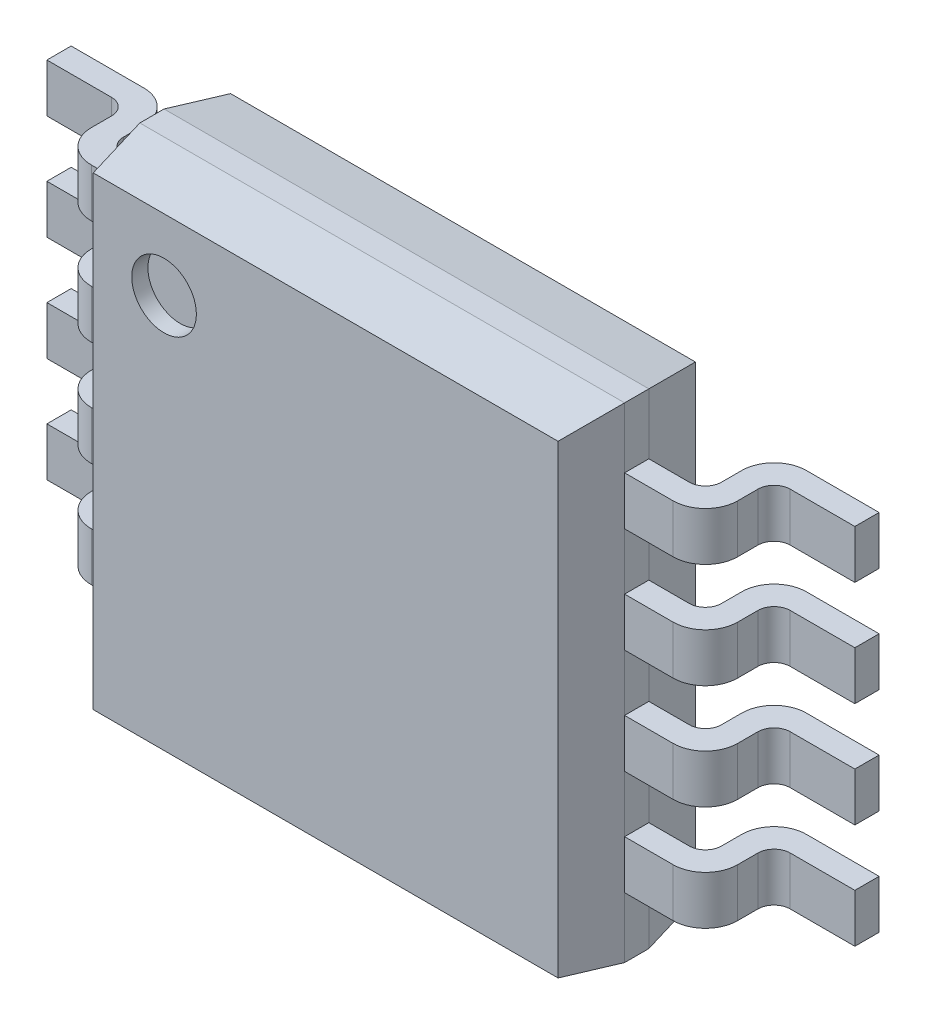
SolidWorks part; units mm, degrees
ref_plane "Спереди" through (0, 0, 0) normal (0, 0, 1) x (1, 0, 0)
ref_plane "Сверху" through (0, 0, 0) normal (0, 1, 0) x (1, 0, 0)
ref_plane "Справа" through (0, 0, 0) normal (1, 0, 0) x (0, 0, -1)
ref_plane "Плоскость1" through (0, 0, 0.075) normal (0, 0, 1) x (1, 0, 0)
sketch "Эскиз1" plane through (0, 0, 0.075) normal (0, 0, 1) x (1, 0, 0)
  line L1 (1.5, 1.5) -> (-1.5, 1.5)
  line L2 (1.5, 1.5) -> (1.5, -1.5)
  line L3 (1.5, -1.5) -> (-1.5, -1.5)
  line L4 (-1.5, 1.5) -> (-1.5, -1.5)
  line L5 (1.5, 1.5) -> (-1.5, -1.5) construction
  line L6 (1.5, -1.5) -> (-1.5, 1.5) construction
  point P0 (0, 0)
extrude "Бобышка-Вытянуть1" add sketch "Эскиз1" along normal blind 0.85
ref_plane "Плоскость2" through (0, 0.975, 0) normal (0, 1, 0) x (-1, 0, 0)
chamfer "Фаска1" distance 0.35 angle 10 8 edges at (0, -1.5, 0.075) (1.5, 0, 0.075) (0, 1.5, 0.075) (-1.5, 0, 0.075) (0, 1.5, 0.925) (1.5, 0, 0.925) (0, -1.5, 0.925) (-1.5, 0, 0.925)
sketch "Эскиз3" plane through (0, 0.975, 0) normal (0, 1, 0) x (-1, 0, 0)
  line L0 (0, -0.8502) -> (0, 2.6313) construction
  line L1 (-1.5, 0.5) -> (1.5, 0.5) construction
  line L2 (-1.5, 0.575) -> (-1.5, 0.425) construction
  line L3 (1.5, 0.575) -> (1.5, 0.425) construction
  line L5 (1.85, 0.325) -> (1.85, 0.2)
  line L6 (2.05, 0) -> (2.5, 0)
  line L7 (2.5, 0) -> (2.5, 0.15)
  line L8 (2.5, 0.15) -> (2.1, 0.15)
  line L9 (2, 0.25) -> (2, 0.375)
  line L10 (-1.5, 0.425) -> (-1.5, 0.575)
  line L11 (-1.5, 0.575) -> (-1.8, 0.575)
  line L12 (-1.5, 0.425) -> (-1.75, 0.425)
  line L13 (-2, 0.25) -> (-2, 0.375)
  line L14 (-2.5, 0.15) -> (-2.1, 0.15)
  line L15 (-2.5, 0) -> (-2.5, 0.15)
  line L16 (-2.05, 0) -> (-2.5, 0)
  line L17 (1.5, 0.425) -> (1.75, 0.425)
  line L18 (1.5, 0.575) -> (1.8, 0.575)
  line L19 (1.5, 0.425) -> (1.5, 0.575)
  line L20 (-1.85, 0.325) -> (-1.85, 0.2)
  arc A0 (1.8, 0.575) -> (2, 0.375) centre (1.8, 0.375) cw
  arc A1 (2.05, 0) -> (1.85, 0.2) centre (2.05, 0.2) cw
  arc A2 (2, 0.25) -> (2.1, 0.15) centre (2.1, 0.25) ccw
  arc A3 (1.75, 0.425) -> (1.85, 0.325) centre (1.75, 0.325) cw
  arc A4 (-1.75, 0.425) -> (-1.85, 0.325) centre (-1.75, 0.325) ccw
  arc A5 (-2, 0.25) -> (-2.1, 0.15) centre (-2.1, 0.25) cw
  arc A6 (-2.05, 0) -> (-1.85, 0.2) centre (-2.05, 0.2) ccw
  arc A7 (-1.8, 0.575) -> (-2, 0.375) centre (-1.8, 0.375) ccw
  dimension "D1" = 0.2
  dimension "D2" = 0.1
extrude "Бобышка-Вытянуть2" add sketch "Эскиз3" along normal blind 0.15 and the other way blind 0.15
pattern_linear "Линейный массив1" count 4 spacing 0.65 along (0, -1, 0) of "Бобышка-Вытянуть2"
sketch "Эскиз4" plane through (0, 0, 0.925) normal (0, 0, 1) x (1, 0, 0)
  circle A0 centre (-1, 1) radius 0.2
extrude "Вырез-Вытянуть1" cut sketch "Эскиз4" against normal blind 0.1
